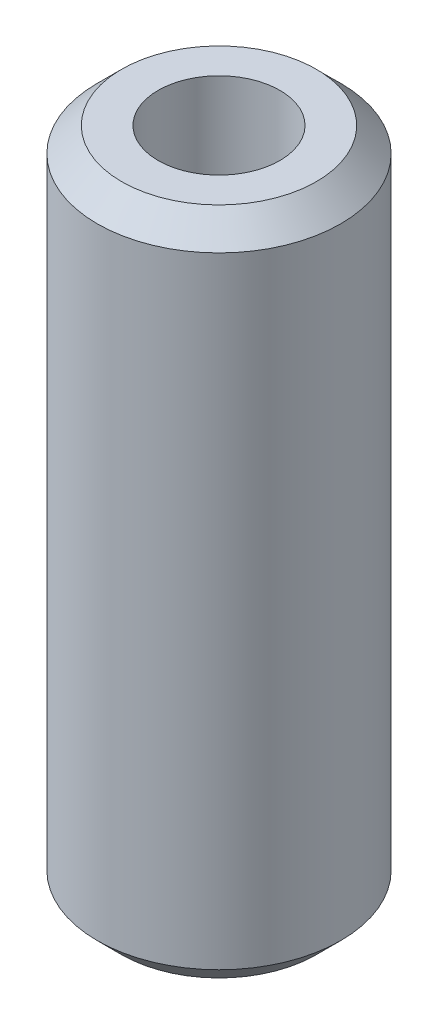
SolidWorks part; units mm, degrees
ref_plane "Front Plane" through (0, 0, 0) normal (0, 0, 1) x (1, 0, 0)
ref_plane "Top Plane" through (0, 0, 0) normal (0, 1, 0) x (1, 0, 0)
ref_plane "Right Plane" through (0, 0, 0) normal (1, 0, 0) x (0, 0, -1)
sketch "Sketch1" plane through (0, 0, 0) normal (0, 1, 0) x (1, 0, 0)
  circle A0 centre (0, 0) radius 6.35
  circle A1 centre (0, 0) radius 12.7
  dimension "D1" = 12.7
  dimension "25.40" = 25.4
extrude "Boss-Extrude1" add sketch "Sketch1" along normal mid plane 69.85
chamfer "Chamfer1" distance 2.54 angle 45 2 edges at (0, -34.925, 12.7) (0, 34.925, 12.7)
